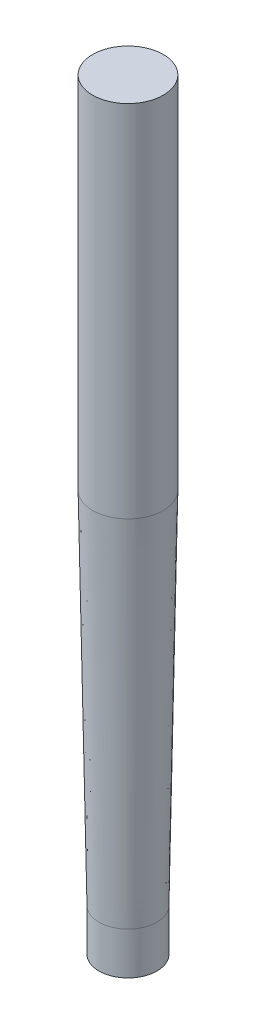
SolidWorks part; units mm, degrees
ref_plane "Front Plane" through (0, 0, 0) normal (0, 0, 1) x (1, 0, 0)
ref_plane "Top Plane" through (0, 0, 0) normal (0, 1, 0) x (1, 0, 0)
ref_plane "Right Plane" through (0, 0, 0) normal (1, 0, 0) x (0, 0, -1)
sketch "Croquis1" plane through (0, 0, 0) normal (1, 0, 0) x (0, 0, -1)
  line L0 (0, -9.0916) -> (0, 85) construction
  line L1 (0, 0) -> (6.8582, 0)
  line L2 (6.8582, 0) -> (8.3418, 85)
  line L3 (8.3418, 85) -> (0, 85)
  line L4 (6.8582, -18.5077) -> (6.8582, 89.8034) construction
  line L5 (8.3418, 85) -> (8.3418, -140.4789) construction
  line L6 (7.6, 42.5) -> (7.6, -100.9101) construction
  line L7 (0, 0) -> (0, 85)
  dimension "D1" = 1
  dimension "D2" = 7.6
  dimension "D3" = 85
revolve "Revolución1" add sketch "Croquis1" angle 360 about L7
sketch "Croquis2" plane through (0, 85, 0) normal (0, 1, 0) x (1, 0, 0)
  circle A1 centre (0, 0) radius 8.3418
  circle A2 centre (0, 0) radius 8.3418
  dimension "D1" = 0
extrude "Saliente-Extruir1" add sketch "Croquis2" along normal blind 85
sketch "Croquis3" plane through (0, 0, 0) normal (0, -1, 0) x (1, 0, 0)
  circle A1 centre (0, 0) radius 6.8582
  circle A2 centre (0, 0) radius 6.8582
  dimension "D1" = 0
extrude "Saliente-Extruir2" add sketch "Croquis3" along normal blind 10
